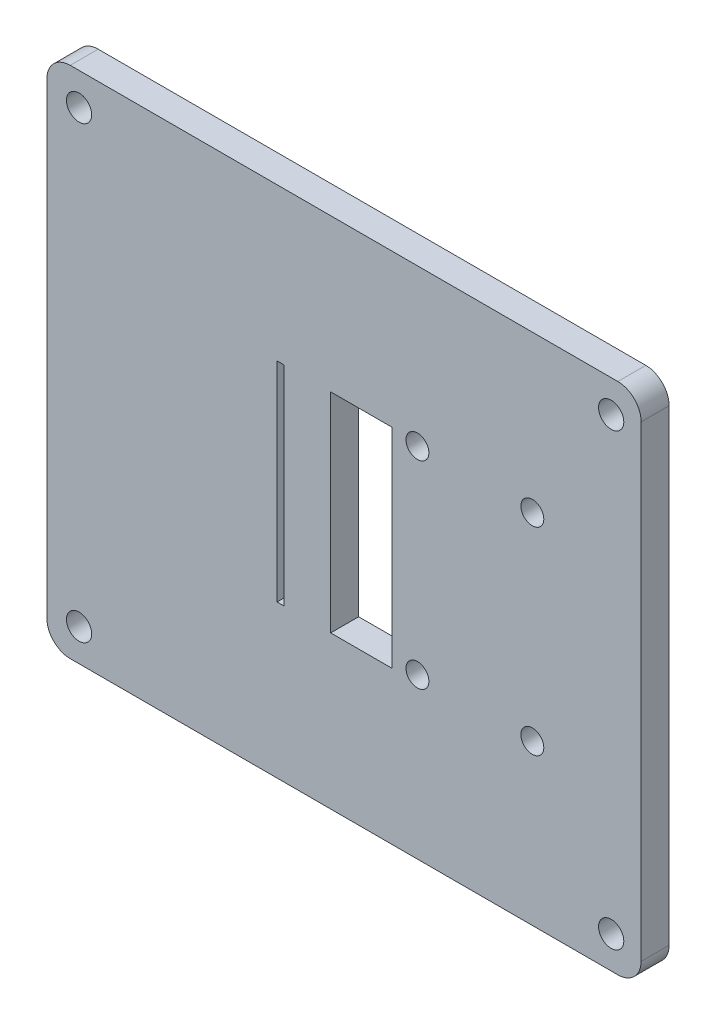
SolidWorks part; units mm, degrees
ref_plane "Front Plane" through (0, 0, 0) normal (0, 0, 1) x (1, 0, 0)
ref_plane "Top Plane" through (0, 0, 0) normal (0, 1, 0) x (1, 0, 0)
ref_plane "Right Plane" through (0, 0, 0) normal (1, 0, 0) x (0, 0, -1)
sketch "Sketch1" plane through (0, 0, 0) normal (0, 0, 1) x (1, 0, 0)
  line L0 (-2.1296, -12.975) -> (62.6404, -12.975) construction
  line L1 (-2.125, 12.025) -> (-2.1343, -37.975) construction
  line L2 (0.875, -40.975) -> (79.875, -40.9843) construction
  line L4 (0.4104, 15.0296) -> (60.1004, 15.0296)
  line L5 (-2.1296, 12.4896) -> (-2.1296, -38.4396)
  line L6 (0.4104, -40.9796) -> (60.1004, -40.9796)
  line L7 (62.6404, 12.4896) -> (62.6404, -38.4396)
  line L9 (40.375, 15.0296) -> (40.375, -40.9796) construction
  line L11 (79.875, 15.025) -> (0.875, 15.0343) construction
  circle A0 centre (1.375, 11.525) radius 1.375
  circle A1 centre (59.375, 11.525) radius 1.375
  circle A2 centre (59.375, -37.475) radius 1.375
  circle A3 centre (1.375, -37.475) radius 1.375
  arc A4 (60.1004, 15.0296) -> (62.6404, 12.4896) centre (60.1004, 12.4896) cw
  arc A5 (62.6404, -38.4396) -> (60.1004, -40.9796) centre (60.1004, -38.4396) cw
  arc A6 (0.4104, -40.9796) -> (-2.1296, -38.4396) centre (0.4104, -38.4396) cw
  arc A7 (-2.1296, 12.4896) -> (0.4104, 15.0296) centre (0.4104, 12.4896) cw
  dimension "D1" = 2.54
  dimension "D2" = 2.75
  dimension "D3" = 2.75
  dimension "D4" = 2.75
  dimension "D5" = 2.75
  dimension "D6" = 64.77
extrude "Boss-Extrude1" add sketch "Sketch1" against normal blind 3.048 contours L5 A6 L6 A5 L7 A4 L4 A7
sketch "Sketch2" plane through (0, 0, 0) normal (0, 0, 1) x (1, 0, 0)
  line L0 (28.8015, -24.3521) -> (35.5015, -24.3521)
  line L1 (28.8015, -24.3521) -> (28.8015, -1.5979)
  line L2 (28.8015, -1.5979) -> (35.5015, -1.5979)
  line L3 (35.5015, -24.3521) -> (35.5015, -1.5979)
  line L4 (-2.1296, 12.4896) -> (-2.1296, -38.4396) construction
  line L5 (62.6404, -38.4396) -> (62.6404, 12.4896) construction
  line L7 (22.9595, -24.3521) -> (23.7215, -24.3521)
  line L8 (35.5015, -12.975) -> (28.8015, -12.975) construction
  line L9 (62.6404, -12.975) -> (-2.1296, -12.975) construction
  line L13 (22.9595, -24.3521) -> (22.9595, -1.5979)
  line L14 (22.9595, -1.5979) -> (23.7215, -1.5979)
  line L15 (23.7215, -24.3521) -> (23.7215, -1.5979)
  line L16 (22.9595, -24.3521) -> (23.7215, -1.5979) construction
  line L17 (22.9595, -1.5979) -> (23.7215, -24.3521) construction
  circle A0 centre (38.2564, -2.0017) radius 1.25
  circle A1 centre (50.78, -2.0017) radius 1.25
  circle A2 centre (50.78, -23.5746) radius 1.25
  circle A3 centre (38.2564, -23.5746) radius 1.25
  point P12 (23.3405, -12.975)
  dimension "D1" = 2.5
  dimension "D2" = 2.5
  dimension "D3" = 2.5
  dimension "D4" = 2.5
  dimension "D5" = 6.7
  dimension "D6" = 22.7542
  dimension "D7" = 24.384
  dimension "D8" = 5.08
  dimension "D9" = 0.762
  dimension "D11" = 2.7549
  dimension "D12" = 0.7775
  dimension "D13" = 21.5729
  dimension "D14" = 12.5236
extrude "Cut-Extrude1" cut sketch "Sketch2" against normal through all
